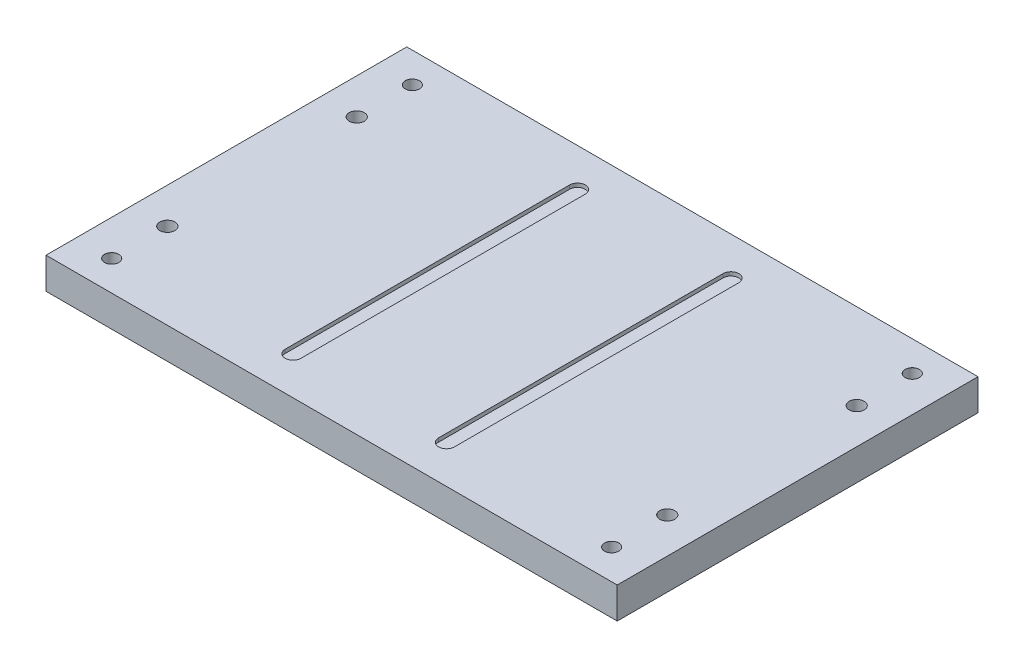
SolidWorks part; units mm, degrees
other "Markup1"
sketch "Sketch4" plane through (-241.3, 26.416, -152.4) normal (0, 1, 0) x (1, 0, 0)
ref_plane "Front Plane" through (0, 0, 0) normal (0, 0, 1) x (1, 0, 0)
ref_plane "Top Plane" through (0, 0, 0) normal (0, 1, 0) x (1, 0, 0)
ref_plane "Right Plane" through (0, 0, 0) normal (1, 0, 0) x (0, 0, -1)
sketch "Sketch1" plane through (0, 0, 0) normal (0, 1, 0) x (1, 0, 0)
  line L1 (-241.3, -152.4) -> (241.3, -152.4)
  line L2 (-241.3, -152.4) -> (-241.3, 152.4)
  line L3 (-241.3, 152.4) -> (241.3, 152.4)
  line L4 (241.3, -152.4) -> (241.3, 152.4)
  line L5 (-241.3, -152.4) -> (241.3, 152.4) construction
  line L6 (-241.3, 152.4) -> (241.3, -152.4) construction
  point P0 (0, 0)
  dimension "D1" = 304.8
  dimension "D2" = 482.6
extrude "Boss-Extrude1" add sketch "Sketch1" along normal blind 26.416
sketch "Sketch2" plane through (0, 26.416, 0) normal (0, 1, 0) x (1, 0, 0)
  line L0 (0, 152.4) -> (0, -152.4) construction
  line L1 (241.3, 152.4) -> (-241.3, 152.4) construction
  line L2 (-241.3, 0) -> (241.3, 0) construction
  line L3 (-241.3, 152.4) -> (-241.3, -152.4) construction
  line L5 (-71.501, -120.142) -> (-58.166, -120.142)
  line L6 (-71.501, -120.142) -> (-71.501, 120.142)
  line L7 (-71.501, 120.142) -> (-58.166, 120.142)
  line L8 (-58.166, -120.142) -> (-58.166, 120.142)
  line L9 (-71.501, -120.142) -> (-58.166, 120.142) construction
  line L10 (-71.501, 120.142) -> (-58.166, -120.142) construction
  line L11 (71.501, 120.142) -> (58.166, 120.142)
  line L12 (58.166, -120.142) -> (58.166, 120.142)
  line L13 (71.501, -120.142) -> (58.166, -120.142)
  line L14 (71.501, -120.142) -> (71.501, 120.142)
  line L15 (-241.3, -152.4) -> (241.3, -152.4) construction
  line L16 (241.3, -152.4) -> (241.3, 152.4) construction
  circle A9 centre (-64.8335, 120.142) radius 6.6675
  circle A10 centre (-64.8335, -120.142) radius 6.6675
  circle A11 centre (64.8335, -120.142) radius 6.6675
  circle A12 centre (64.8335, 120.142) radius 6.6675
  point P9 (-64.8335, 0)
  dimension "D4" = 13.335
  dimension "D1" = 13.335
  dimension "D2" = 240.284
  dimension "D3" = 116.332
extrude "Cut-Extrude3" cut sketch "Sketch2" along direction (0, -1, 0) on the side against the normal blind 3.175 contours L6 A10 L8 A9 | L7 A9 | A10 L5 | A10 L5 | L7 A9 | A12 L11 | A12 L11 | L14 A12 L12 A11 | L13 A11 | L13 A11
sketch "Sketch3" plane through (0, 26.416, 0) normal (0, 1, 0) x (1, 0, 0)
  line L7 (-241.3, 152.4) -> (-241.3, -152.4) construction
  line L8 (0, 152.4) -> (0, -152.4) construction
  line L9 (241.3, 152.4) -> (-241.3, 152.4) construction
  line L10 (-241.3, 0) -> (241.3, 0) construction
  line L23 (-241.3, -152.4) -> (241.3, -152.4) construction
  line L24 (241.3, -152.4) -> (241.3, 152.4) construction
  line L25 (-236.601, -67.31) -> (-71.501, -67.31) construction
  line L26 (-236.601, -67.31) -> (-236.601, -92.71) construction
  line L27 (-236.601, -92.71) -> (-71.501, -92.71) construction
  line L28 (-71.501, -67.31) -> (-71.501, -92.71) construction
  line L29 (-154.051, -92.71) -> (-154.051, -67.31) construction
  line L30 (-236.601, -80.01) -> (-71.501, -80.01) construction
  line L33 (-71.501, 120.142) -> (-71.501, -120.142)
  line L34 (-58.166, -120.142) -> (-58.166, 120.142)
  line L35 (-71.501, 120.142) -> (-71.501, -120.142) construction
  line L36 (-58.166, -120.142) -> (-58.166, 120.142) construction
  circle A8 centre (0, 0) radius 37.465 construction
  circle A9 centre (-211.201, -80.01) radius 6.35
  arc A15 (-58.166, 120.142) -> (-71.501, 120.142) centre (-64.8335, 120.142) ccw
  arc A16 (-71.501, -120.142) -> (-58.166, -120.142) centre (-64.8335, -120.142) ccw
  arc A17 (-58.166, 120.142) -> (-71.501, 120.142) centre (-64.8335, 120.142) ccw construction
  arc A18 (-71.501, -120.142) -> (-58.166, -120.142) centre (-64.8335, -120.142) ccw construction
  circle A20 centre (-211.201, 80.01) radius 6.35
  circle A22 centre (211.201, -80.01) radius 6.35
  circle A24 centre (211.201, 80.01) radius 6.35
  circle A25 centre (-211.201, -127) radius 2.54
  circle A26 centre (-211.201, 127) radius 2.54
  circle A27 centre (211.201, -127) radius 2.54
  circle A28 centre (211.201, 127) radius 2.54
  point P0 (-154.051, -80.01)
  dimension "D5" = 160.02
  dimension "D6" = 46.99
  dimension "D7" = 25.4
  dimension "D8" = 74.93
  dimension "D9" = 25.4
  dimension "D4" = 0
  dimension "D1" = 12.7
  dimension "D2" = 25.4
  dimension "D3" = 165.1
  dimension "D10" = 0
extrude "Cut-Extrude2" cut sketch "Sketch3" against normal through all
hole_wizard "M10 Clearance Hole2" positions "Sketch9" profile "Sketch10" hole size "M10" standard "ANSI Metric" end condition through all
sketch "Sketch9" plane through (0, 26.416, 0) normal (0, 1, 0) x (1, 0, 0)
  point P0 (-211.201, -127)
sketch "Sketch10" plane through (-211.201, 26.416, 127) normal (1, 0, 0) x (0, 0, 1)
  line L0 (0, 0) -> (0, 26.416)
  line L1 (0, 26.416) -> (6, 26.416)
  line L2 (6, 26.416) -> (6, 0.025)
  line L3 (6, 0.025) -> (6.025, 0)
  line L5 (6.025, 0) -> (0, 0)
  line L6 (-6, 0.025) -> (-6.025, 0) construction
  line L11 (0, -6.35) -> (0, 107.95) construction
  dimension "Thru Hole Dia." = 12
  dimension "Thru Hole Depth" = 26.416
  dimension "Near C'Sink Dia." = 12.05
  dimension "Near C'Sink Angle" = 90
hole_wizard "M10 Clearance Hole3" positions "Sketch11" profile "Sketch12" hole size "M10" standard "ANSI Metric" end condition through all
sketch "Sketch11" plane through (0, 26.416, 0) normal (0, 1, 0) x (1, 0, 0)
  point P0 (-211.201, 127)
  point P3 (211.201, 127)
  point P6 (211.201, -127)
sketch "Sketch12" plane through (-211.201, 26.416, -127) normal (1, 0, 0) x (0, 0, 1)
  line L0 (0, 0) -> (0, 26.416)
  line L1 (0, 26.416) -> (6, 26.416)
  line L2 (6, 26.416) -> (6, 0.025)
  line L3 (6, 0.025) -> (6.025, 0)
  line L5 (6.025, 0) -> (0, 0)
  line L6 (-6, 0.025) -> (-6.025, 0) construction
  line L11 (0, -6.35) -> (0, 107.95) construction
  dimension "Thru Hole Dia." = 12
  dimension "Thru Hole Depth" = 26.416
  dimension "Near C'Sink Dia." = 12.05
  dimension "Near C'Sink Angle" = 90
